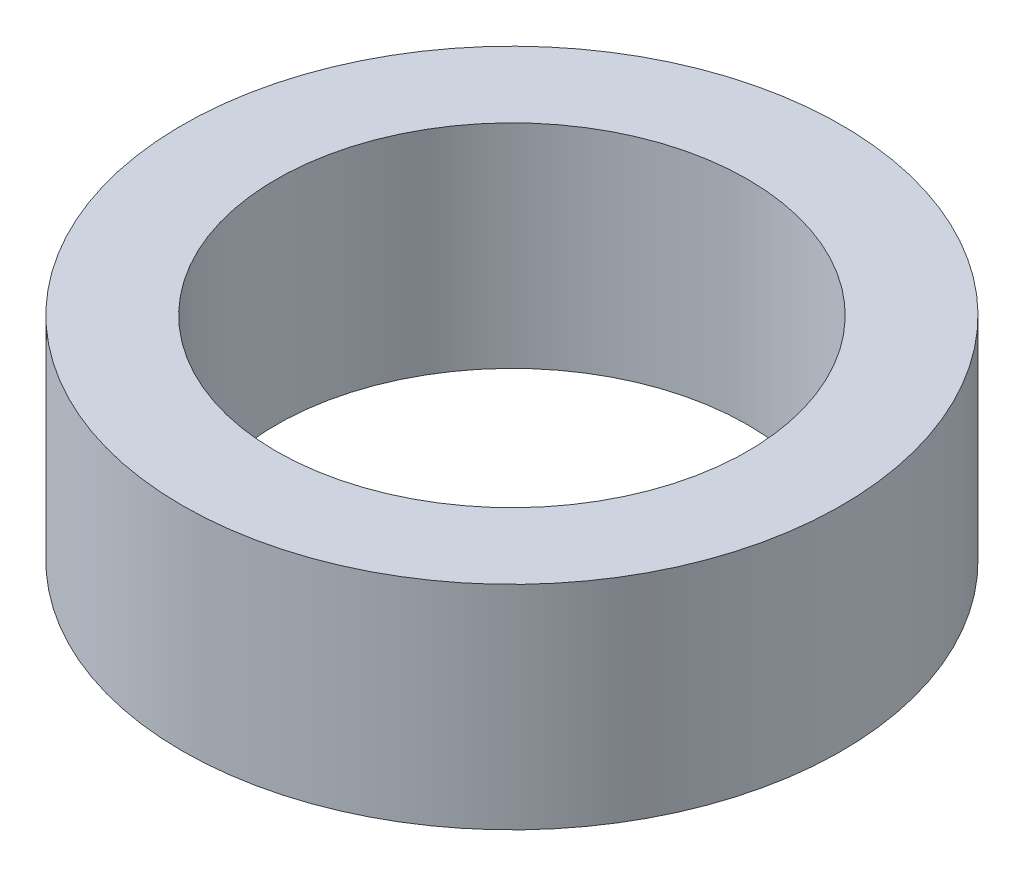
SolidWorks part; units mm, degrees
ref_plane "Front Plane" through (0, 0, 0) normal (0, 0, 1) x (1, 0, 0)
ref_plane "Top Plane" through (0, 0, 0) normal (0, 1, 0) x (1, 0, 0)
ref_plane "Right Plane" through (0, 0, 0) normal (1, 0, 0) x (0, 0, -1)
sketch "Sketch1" plane through (0, 0, 0) normal (0, 1, 0) x (1, 0, 0)
  circle A0 centre (0, 0) radius 3.325
  circle A1 centre (0, 0) radius 4.65
  dimension "D1" = 6.65
  dimension "D2" = 9.3
extrude "Boss-Extrude1" add sketch "Sketch1" along normal blind 3
